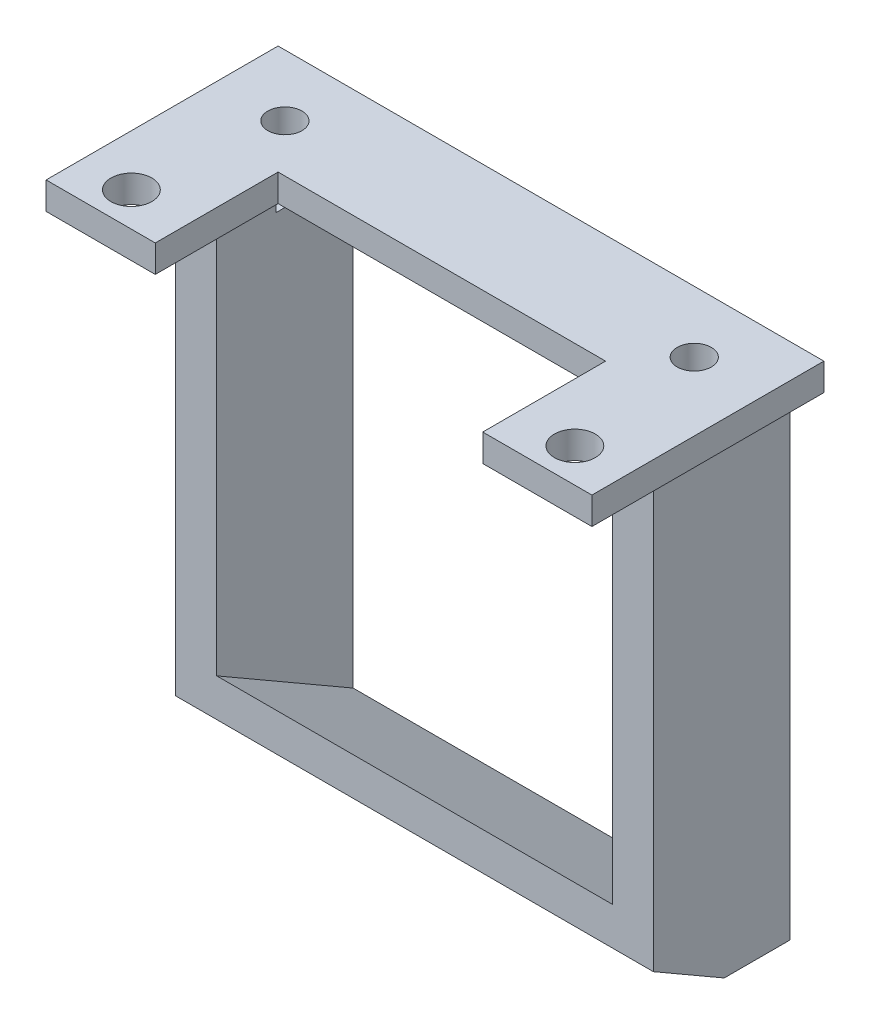
SolidWorks part; units mm, degrees
ref_plane "Front Plane" through (0, 0, 0) normal (0, 0, 1) x (1, 0, 0)
ref_plane "Top Plane" through (0, 0, 0) normal (0, 1, 0) x (1, 0, 0)
ref_plane "Right Plane" through (0, 0, 0) normal (1, 0, 0) x (0, 0, -1)
sketch "Sketch1" plane through (0, 0, 0) normal (0, 1, 0) x (1, 0, 0)
  line L1 (-21.714, 13.5141) -> (-13.714, 13.5141)
  line L2 (-21.714, 13.5141) -> (-21.714, -3.4859)
  line L3 (-21.714, -3.4859) -> (-13.714, -3.4859)
  line L4 (-13.714, 13.5141) -> (-13.714, -3.4859)
  line L5 (10.286, 13.5141) -> (18.286, 13.5141)
  line L6 (10.286, 13.5141) -> (10.286, -3.4859)
  line L7 (10.286, -3.4859) -> (18.286, -3.4859)
  line L8 (18.286, 13.5141) -> (18.286, -3.4859)
  line L9 (-13.714, 13.5141) -> (10.286, 13.5141)
  line L10 (-13.714, 13.5141) -> (-13.714, 5.5141)
  line L11 (-13.714, 5.5141) -> (10.286, 5.5141)
  line L12 (10.286, 13.5141) -> (10.286, 5.5141)
  dimension "D1" = 17
  dimension "D2" = 8
  dimension "D3" = 17
  dimension "D4" = 8
  dimension "D5" = 40
  dimension "D6" = 0
  dimension "D7" = 8
  dimension "D8" = 0
  dimension "D9" = 0
  dimension "D10" = 0
extrude "Boss-Extrude1" add sketch "Sketch1" against normal blind 2 contours L4 L1 L2 L3 | L4 L11 L6 L9 | L8 L5 L6 L7
sketch "Sketch4" plane through (0, -2, 0) normal (0, -1, 0) x (-1, 0, 0)
  line L0 (-18.286, 13.5141) -> (-18.286, -3.4859) construction
  line L1 (-15.786, 13.5141) -> (-12.786, 13.5141)
  line L2 (-15.786, 13.5141) -> (-15.786, 3.5141)
  line L3 (-15.786, 3.5141) -> (-12.786, 3.5141)
  line L4 (-12.786, 13.5141) -> (-12.786, 3.5141)
  line L5 (16.214, 13.5141) -> (19.214, 13.5141)
  line L6 (16.214, 13.5141) -> (16.214, 3.5141)
  line L7 (16.214, 3.5141) -> (19.214, 3.5141)
  line L8 (19.214, 13.5141) -> (19.214, 3.5141)
  line L9 (21.714, 13.5141) -> (-18.286, 13.5141) construction
  dimension "D1" = 10
  dimension "D2" = 3
  dimension "D3" = 3
  dimension "D4" = 10
  dimension "D5" = 29
  dimension "D6" = 2.5
  dimension "D7" = 0
  dimension "D8" = 0
extrude "Boss-Extrude4" add sketch "Sketch4" along normal blind 36
sketch "Sketch5" plane through (12.786, 0, 0) normal (-1, 0, 0) x (0, 0, 1)
  line L0 (-13.5141, -38) -> (-3.5141, -32.2265)
  line L1 (-3.5141, -32.2265) -> (-3.5141, -38)
  line L2 (-3.5141, -38) -> (-13.5141, -38)
  line L3 (-3.5141, -38) -> (-13.5141, -38) construction
  line L4 (-3.5141, -38) -> (-3.5141, -2) construction
  point P2 (0, 0)
  point P5 (0, 0)
  point P8 (0, 0)
  point P10 (0, 0)
  dimension "D1" = 30
extrude "Boss-Extrude5" add sketch "Sketch5" along normal up to next contours L1 L2 L0
sketch "Sketch6" plane through (-19.214, 0, 0) normal (-1, 0, 0) x (0, 0, 1)
  line L0 (-3.5141, -38) -> (-3.5141, -35)
  line L1 (-3.5141, -38) -> (-8.7102, -38)
  line L2 (-3.5141, -35) -> (-8.7102, -38)
  line L4 (-3.5141, -38) -> (-13.5141, -38) construction
  line L5 (-3.5141, -38) -> (-3.5141, -2) construction
  point P2 (0, 0)
  point P3 (0, 0)
  point P8 (0, 0)
  point P10 (0, 0)
  dimension "D1" = 30
  dimension "D2" = 3
extrude "Cut-Extrude3" cut sketch "Sketch6" against normal through all
sketch "Sketch7" plane through (0, 0, 0) normal (0, 1, 0) x (1, 0, 0)
  line L1 (-21.714, 13.5141) -> (-21.714, -3.4859) construction
  line L2 (-21.714, -3.4859) -> (-13.714, -3.4859) construction
  line L3 (10.286, -3.4859) -> (18.286, -3.4859) construction
  circle A0 centre (-16.714, 9.0141) radius 1.25
  circle A1 centre (13.286, 9.0141) radius 1.25
  circle A2 centre (-17.964, -0.9859) radius 1.5
  circle A3 centre (14.536, -0.9859) radius 1.5
  point P8 (13.712, 2.1396)
  point P9 (13.712, 2.1396)
  point P14 (-50.6101, 4.4375)
  dimension "D1" = 3
  dimension "D2" = 3
  dimension "D3" = 2.5
  dimension "D4" = 2.5
  dimension "D12" = 2.5
  dimension "D5" = 30
  dimension "D6" = 32.5
  dimension "D7" = 10
  dimension "D8" = 10
  dimension "D9" = 3.75
  dimension "D10" = 2.5
  dimension "D11" = 5
extrude "Cut-Extrude4" cut sketch "Sketch7" against normal blind 5
